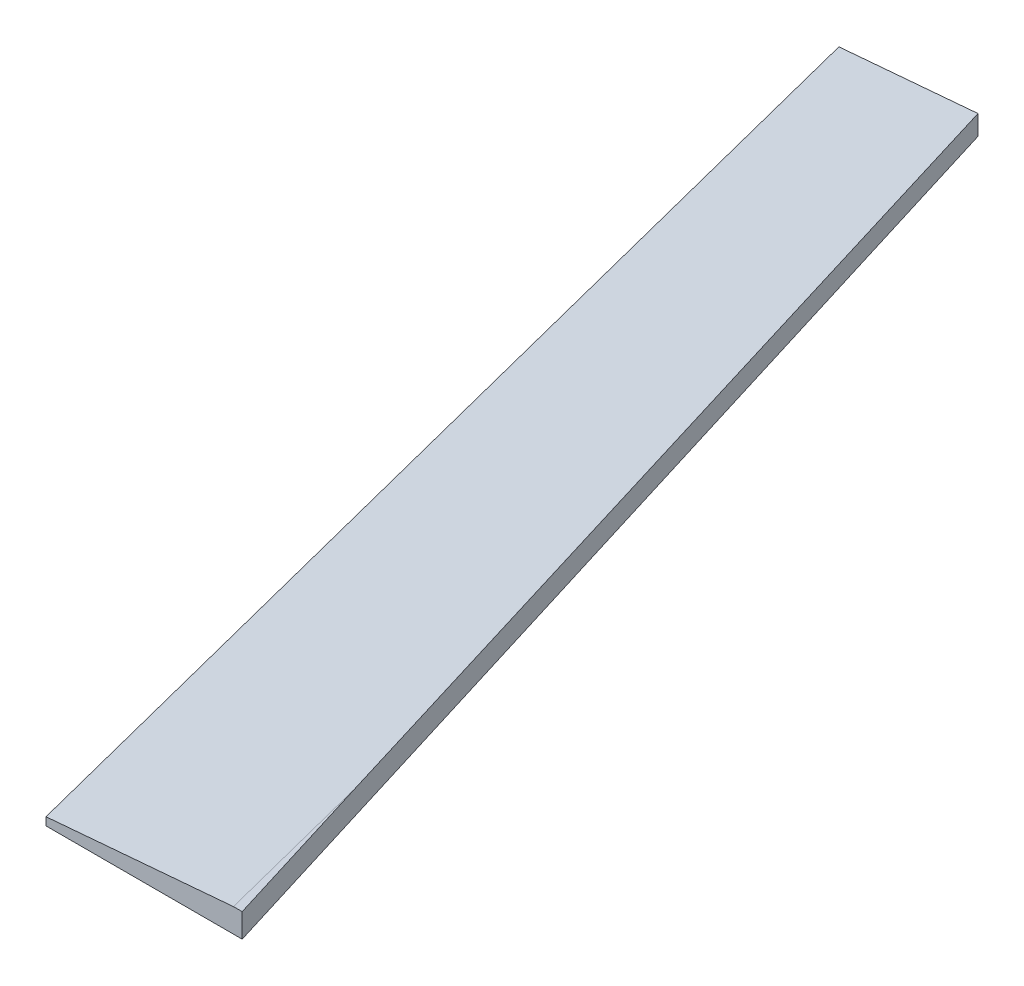
SolidWorks part; units mm, degrees
ref_plane "Front Plane" through (0, 0, 0) normal (0, 0, 1) x (1, 0, 0)
ref_plane "Top Plane" through (0, 0, 0) normal (0, 1, 0) x (1, 0, 0)
ref_plane "Right Plane" through (0, 0, 0) normal (1, 0, 0) x (0, 0, -1)
sketch "Sketch2" plane through (0, 0, 0) normal (0, 1, 0) x (1, 0, 0)
  line L0 (126.5816, -16.6788) -> (178.9026, -186.602)
  line L1 (178.9026, -186.602) -> (147.5508, -186.602)
  line L2 (126.5816, -16.6788) -> (104.35, -16.6788)
  line L3 (104.35, -16.6788) -> (147.5508, -186.602)
extrude "Boss-Extrude1" add sketch "Sketch2" along normal blind 3.81
chamfer "Chamfer1" distance 2.54 angle 85 1 edges at (125.9504, 3.81, 101.6404)
